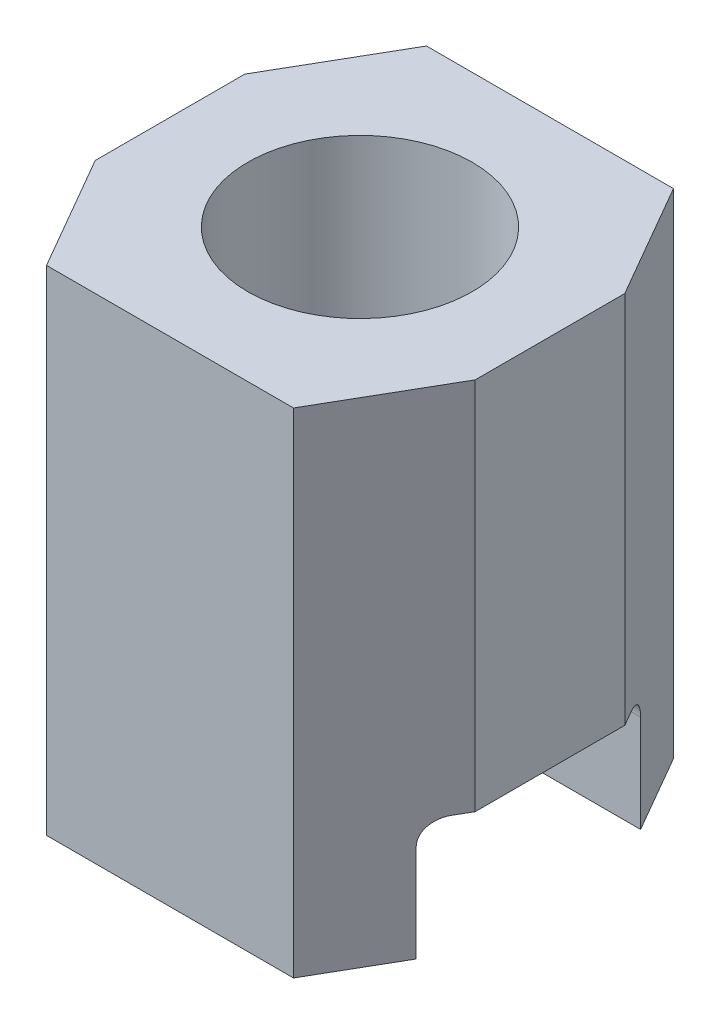
SolidWorks part; units mm, degrees
ref_plane "Front Plane" through (0, 0, 0) normal (0, 0, 1) x (1, 0, 0)
ref_plane "Top Plane" through (0, 0, 0) normal (0, 1, 0) x (1, 0, 0)
ref_plane "Right Plane" through (0, 0, 0) normal (1, 0, 0) x (0, 0, -1)
sketch "Sketch1" plane through (0, 0, 0) normal (0, 1, 0) x (1, 0, 0)
  line L0 (-0.8254, 1.27) -> (0.8254, 1.27)
  line L1 (0.8254, 1.27) -> (1.27, 0.5)
  line L2 (1.27, 0.5) -> (1.27, -0.5)
  line L3 (1.27, -0.5) -> (0.8254, -1.27)
  line L4 (0.8254, -1.27) -> (-0.8254, -1.27)
  line L5 (-0.8254, -1.27) -> (-1.27, -0.5)
  line L6 (-1.27, -0.5) -> (-1.27, 0.5)
  line L7 (-1.27, 0.5) -> (-0.8254, 1.27)
  line L8 (0, 0) -> (-1.27, 0) construction
  line L9 (0, 0) -> (0, 1.27) construction
  circle A0 centre (0, 0) radius 0.675
  dimension "D1" = 1.35
  dimension "D2" = 1
  dimension "D3" = 2.54
  dimension "D4" = 2.54
  dimension "D5" = 120
extrude "Boss-Extrude1" add sketch "Sketch1" along normal blind 3.3
sketch "Sketch2" plane through (-1.27, 0, 0) normal (-1, 0, 0) x (0, 0, 1)
  line L0 (-1.27, 0) -> (-0.5, 0) construction
  line L1 (-0.75, 0) -> (0.75, 0)
  line L2 (-0.75, 0) -> (-0.75, 0.65)
  line L3 (-0.6, 0.8) -> (0.6, 0.8)
  line L4 (0.75, 0) -> (0.75, 0.65)
  arc A0 (0.6, 0.8) -> (0.75, 0.65) centre (0.6, 0.65) cw
  arc A1 (-0.75, 0.65) -> (-0.6, 0.8) centre (-0.6, 0.65) cw
  dimension "D4" = 0.15
  dimension "D1" = 1.5
  dimension "D2" = 0.8
  dimension "D3" = 0.75
extrude "Cut-Extrude1" cut sketch "Sketch2" against normal up to next
sketch "Sketch3" plane through (0, 3.3, 0) normal (0, 1, 0) x (1, 0, 0)
  circle A0 centre (0, 0) radius 0.75
  dimension "D1" = 1.5
extrude "Cut-Extrude2" cut sketch "Sketch3" against normal blind 2
